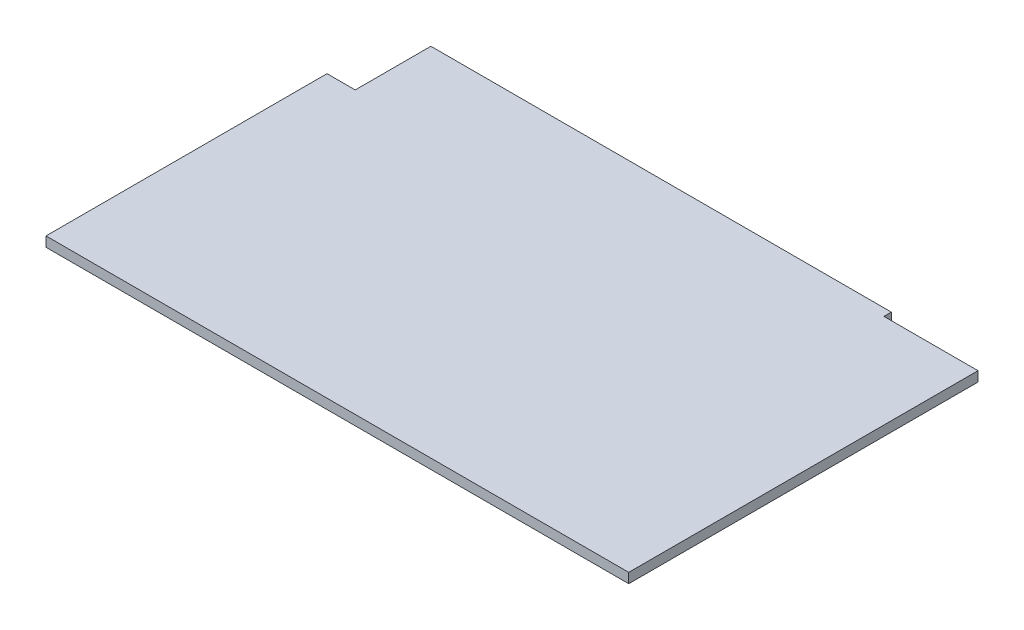
SolidWorks part; units mm, degrees
ref_plane "Front Plane" through (0, 0, 0) normal (0, 0, 1) x (1, 0, 0)
ref_plane "Top Plane" through (0, 0, 0) normal (0, 1, 0) x (1, 0, 0)
ref_plane "Right Plane" through (0, 0, 0) normal (1, 0, 0) x (0, 0, -1)
sketch "Sketch1" plane through (0, 0, 0) normal (0, 1, 0) x (1, 0, 0)
  line L0 (0, 0) -> (0, 75.95)
  line L1 (0, 75.95) -> (7.62, 75.95)
  line L2 (7.62, 75.95) -> (7.62, 96.4)
  line L3 (7.62, 96.4) -> (132.07, 96.4)
  line L4 (132.07, 96.4) -> (132.07, 94.4)
  line L5 (132.07, 94.4) -> (157.49, 94.4)
  line L6 (157.49, 94.4) -> (157.49, 0)
  line L13 (157.49, 0) -> (0, 0)
  point P5 (0, 0)
  dimension "D1" = 2
  dimension "D2" = 157.49
  dimension "D8" = 75.95
  dimension "D9" = 7.62
  dimension "D10" = 132.07
  dimension "D11" = 96.4
extrude "Boss-Extrude1" add sketch "Sketch1" along normal blind 2.67
